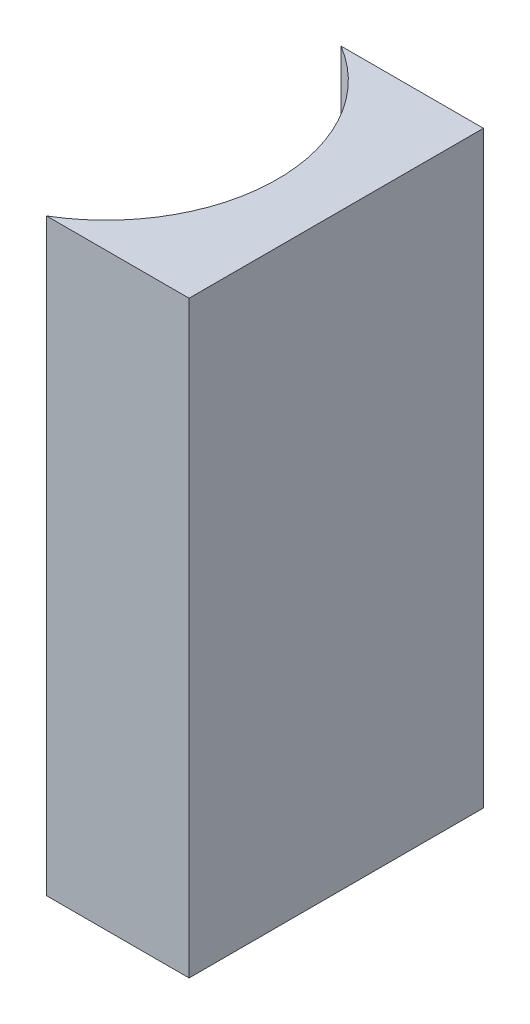
SolidWorks part; units mm, degrees
ref_plane "前视基准面" through (0, 0, 0) normal (0, 0, 1) x (1, 0, 0)
ref_plane "上视基准面" through (0, 0, 0) normal (0, 1, 0) x (1, 0, 0)
ref_plane "右视基准面" through (0, 0, 0) normal (1, 0, 0) x (0, 0, -1)
sketch "草图1" plane through (0, 0, 0) normal (0, 1, 0) x (1, 0, 0)
  line L0 (0, 0) -> (0, -10)
  line L1 (0, 0) -> (-4.8413, 0)
  line L2 (0, -10) -> (-4.8413, -10)
  line L3 (21.2259, -5) -> (-21.2259, -5) construction
  arc A0 (-4.8413, -10) -> (-4.8413, 0) centre (-7.82, -5) ccw
  point P7 (-2, -5)
  point P8 (0, -5)
  dimension "D2" = 5.82
  dimension "D3" = 2
  dimension "D1" = 10
extrude "凸台-拉伸1" add sketch "草图1" along normal blind 20
